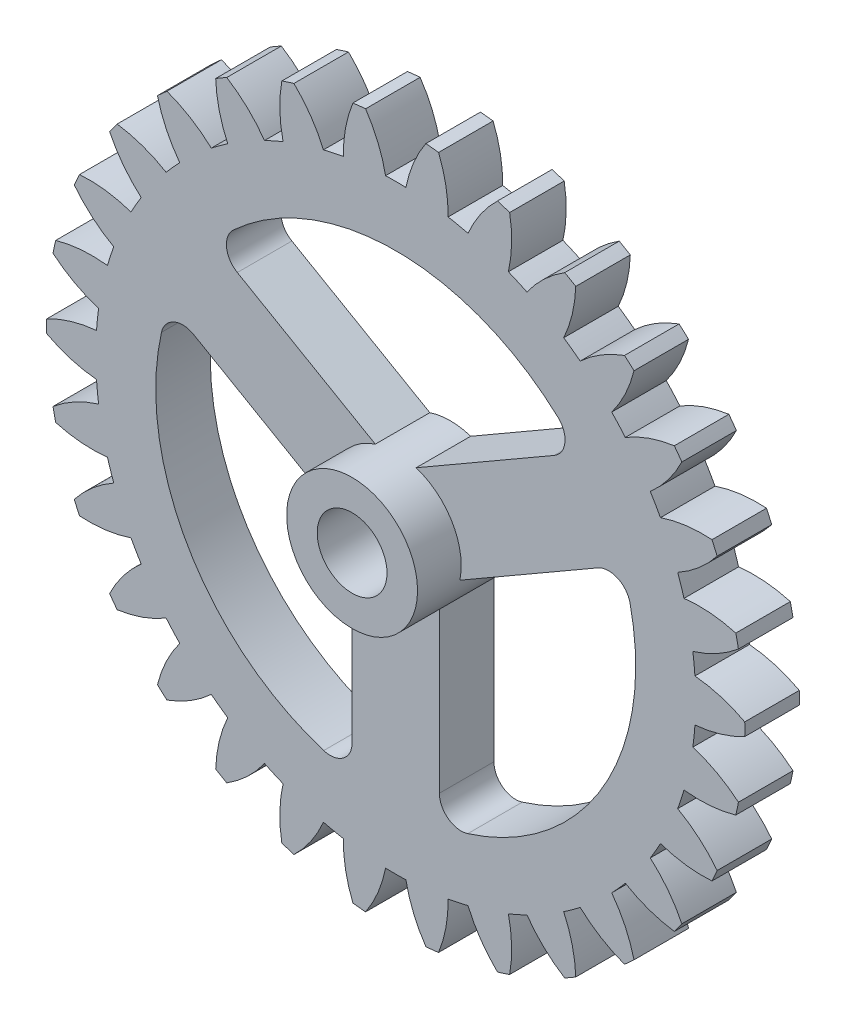
SolidWorks part; units mm, degrees
ref_plane "Front Plane" through (0, 0, 0) normal (0, 0, 1) x (1, 0, 0)
ref_plane "Top Plane" through (0, 0, 0) normal (0, 1, 0) x (1, 0, 0)
ref_plane "Right Plane" through (0, 0, 0) normal (1, 0, 0) x (0, 0, -1)
sketch "Sketch1" plane through (0, 0, 0) normal (0, 0, 1) x (1, 0, 0)
  arc A0 (-15.9973, -0.2927) -> (-13.7146, -0.9725) centre (-13.1775, 5.0034) ccw
  arc A1 (-13.7146, -0.9725) -> (-13.6171, -1.9002) centre (0, 0) ccw
  arc A2 (-13.6171, -1.9002) -> (-15.7086, -3.0398) centre (-11.8492, -7.6338) ccw
  arc A3 (-15.7086, -3.0398) -> (-15.5869, -3.6123) centre (0, 0) ccw
  arc A4 (-15.5869, -3.6123) -> (-13.2127, -3.8027) centre (-13.9298, 2.1543) ccw
  arc A5 (-13.2127, -3.8027) -> (-12.9244, -4.6898) centre (0, 0) ccw
  arc A6 (-12.9244, -4.6898) -> (-14.7333, -6.2393) centre (-10.0031, -9.9306) ccw
  arc A7 (-14.7333, -6.2393) -> (-14.4952, -6.7741) centre (0, 0) ccw
  arc A8 (-14.4952, -6.7741) -> (-12.1333, -6.4666) centre (-14.0733, -0.7889) ccw
  arc A9 (-12.1333, -6.4666) -> (-11.6669, -7.2745) centre (0, 0) ccw
  arc A10 (-11.6669, -7.2745) -> (-13.1141, -9.1662) centre (-7.7199, -11.7934) ccw
  arc A11 (-13.1141, -9.1662) -> (-12.7701, -9.6398) centre (0, 0) ccw
  arc A12 (-12.7701, -9.6398) -> (-10.5237, -8.848) centre (-13.6017, -3.6977) ccw
  arc A13 (-10.5237, -8.848) -> (-9.8995, -9.5412) centre (0, 0) ccw
  arc A14 (-9.8995, -9.5412) -> (-10.9218, -11.6925) centre (-5.0992, -13.1407) ccw
  arc A15 (-10.9218, -11.6925) -> (-10.4868, -12.0842) centre (0, 0) ccw
  arc A16 (-10.4868, -12.0842) -> (-8.4541, -10.8426) centre (-12.5357, -6.4448) ccw
  arc A17 (-8.4541, -10.8426) -> (-7.6995, -11.3909) centre (0, 0) ccw
  arc A18 (-7.6995, -11.3909) -> (-8.2521, -13.7078) centre (-2.2556, -13.9137) ccw
  arc A19 (-8.2521, -13.7078) -> (-7.7452, -14.0004) centre (0, 0) ccw
  arc A20 (-7.7452, -14.0004) -> (-6.0151, -12.3634) centre (-10.9218, -8.9103) ccw
  arc A21 (-6.0151, -12.3634) -> (-5.1629, -12.7428) centre (0, 0) ccw
  arc A22 (-5.1629, -12.7428) -> (-5.2218, -15.1239) centre (0.6865, -14.0787) ccw
  arc A23 (-5.2218, -15.1239) -> (-4.6651, -15.3048) centre (0, 0) ccw
  arc A24 (-4.6651, -15.3048) -> (-3.3131, -13.3438) centre (-8.8306, -10.9864) ccw
  arc A25 (-3.3131, -13.3438) -> (-2.4007, -13.5378) centre (0, 0) ccw
  arc A26 (-2.4007, -13.5378) -> (-1.9632, -15.8791) centre (3.5986, -13.6283) ccw
  arc A27 (-1.9632, -15.8791) -> (-1.3811, -15.9403) centre (0, 0) ccw
  arc A28 (-1.3811, -15.9403) -> (-0.4664, -13.7411) centre (-6.3534, -12.5823) ccw
  arc A29 (-0.4664, -13.7411) -> (0.4664, -13.7411) centre (0, 0) ccw
  arc A30 (0.4664, -13.7411) -> (1.3811, -15.9403) centre (6.3534, -12.5823) ccw
  arc A31 (1.3811, -15.9403) -> (1.9632, -15.8791) centre (0, 0) ccw
  arc A32 (1.9632, -15.8791) -> (2.4007, -13.5378) centre (-3.5986, -13.6283) ccw
  arc A33 (2.4007, -13.5378) -> (3.3131, -13.3438) centre (0, 0) ccw
  arc A34 (3.3131, -13.3438) -> (4.6651, -15.3048) centre (8.8306, -10.9864) ccw
  arc A35 (4.6651, -15.3048) -> (5.2218, -15.1239) centre (0, 0) ccw
  arc A36 (5.2218, -15.1239) -> (5.1629, -12.7428) centre (-0.6865, -14.0787) ccw
  arc A37 (5.1629, -12.7428) -> (6.0151, -12.3634) centre (0, 0) ccw
  arc A38 (6.0151, -12.3634) -> (7.7452, -14.0004) centre (10.9218, -8.9103) ccw
  arc A39 (7.7452, -14.0004) -> (8.2521, -13.7078) centre (0, 0) ccw
  arc A40 (8.2521, -13.7078) -> (7.6995, -11.3909) centre (2.2556, -13.9137) ccw
  arc A41 (7.6995, -11.3909) -> (8.4541, -10.8426) centre (0, 0) ccw
  arc A42 (8.4541, -10.8426) -> (10.4868, -12.0842) centre (12.5357, -6.4448) ccw
  arc A43 (10.4868, -12.0842) -> (10.9218, -11.6925) centre (0, 0) ccw
  arc A44 (10.9218, -11.6925) -> (9.8995, -9.5412) centre (5.0992, -13.1407) ccw
  arc A45 (9.8995, -9.5412) -> (10.5237, -8.848) centre (0, 0) ccw
  arc A46 (10.5237, -8.848) -> (12.7701, -9.6398) centre (13.6017, -3.6977) ccw
  arc A47 (12.7701, -9.6398) -> (13.1141, -9.1662) centre (0, 0) ccw
  arc A48 (13.1141, -9.1662) -> (11.6669, -7.2745) centre (7.7199, -11.7934) ccw
  arc A49 (11.6669, -7.2745) -> (12.1333, -6.4666) centre (0, 0) ccw
  arc A50 (12.1333, -6.4666) -> (14.4952, -6.7741) centre (14.0733, -0.7889) ccw
  arc A51 (14.4952, -6.7741) -> (14.7333, -6.2393) centre (0, 0) ccw
  arc A52 (14.7333, -6.2393) -> (12.9244, -4.6898) centre (10.0031, -9.9306) ccw
  arc A53 (12.9244, -4.6898) -> (13.2127, -3.8027) centre (0, 0) ccw
  arc A54 (13.2127, -3.8027) -> (15.5869, -3.6123) centre (13.9298, 2.1543) ccw
  arc A55 (15.5869, -3.6123) -> (15.7086, -3.0398) centre (0, 0) ccw
  arc A56 (15.7086, -3.0398) -> (13.6171, -1.9002) centre (11.8492, -7.6338) ccw
  arc A57 (13.6171, -1.9002) -> (13.7146, -0.9725) centre (0, 0) ccw
  arc A58 (13.7146, -0.9725) -> (15.9973, -0.2927) centre (13.1775, 5.0034) ccw
  arc A59 (15.9973, -0.2927) -> (15.9973, 0.2927) centre (0, 0) ccw
  arc A60 (15.9973, 0.2927) -> (13.7146, 0.9725) centre (13.1775, -5.0034) ccw
  arc A61 (13.7146, 0.9725) -> (13.6171, 1.9002) centre (0, 0) ccw
  arc A62 (13.6171, 1.9002) -> (15.7086, 3.0398) centre (11.8492, 7.6338) ccw
  arc A63 (15.7086, 3.0398) -> (15.5869, 3.6123) centre (0, 0) ccw
  arc A64 (15.5869, 3.6123) -> (13.2127, 3.8027) centre (13.9298, -2.1543) ccw
  arc A65 (13.2127, 3.8027) -> (12.9244, 4.6898) centre (0, 0) ccw
  arc A66 (12.9244, 4.6898) -> (14.7333, 6.2393) centre (10.0031, 9.9306) ccw
  arc A67 (14.7333, 6.2393) -> (14.4952, 6.7741) centre (0, 0) ccw
  arc A68 (14.4952, 6.7741) -> (12.1333, 6.4666) centre (14.0733, 0.7889) ccw
  arc A69 (12.1333, 6.4666) -> (11.6669, 7.2745) centre (0, 0) ccw
  arc A70 (11.6669, 7.2745) -> (13.1141, 9.1662) centre (7.7199, 11.7934) ccw
  arc A71 (13.1141, 9.1662) -> (12.7701, 9.6398) centre (0, 0) ccw
  arc A72 (12.7701, 9.6398) -> (10.5237, 8.848) centre (13.6017, 3.6977) ccw
  arc A73 (10.5237, 8.848) -> (9.8995, 9.5412) centre (0, 0) ccw
  arc A74 (9.8995, 9.5412) -> (10.9218, 11.6925) centre (5.0992, 13.1407) ccw
  arc A75 (10.9218, 11.6925) -> (10.4868, 12.0842) centre (0, 0) ccw
  arc A76 (10.4868, 12.0842) -> (8.4541, 10.8426) centre (12.5357, 6.4448) ccw
  arc A77 (8.4541, 10.8426) -> (7.6995, 11.3909) centre (0, 0) ccw
  arc A78 (7.6995, 11.3909) -> (8.2521, 13.7078) centre (2.2556, 13.9137) ccw
  arc A79 (8.2521, 13.7078) -> (7.7452, 14.0004) centre (0, 0) ccw
  arc A80 (7.7452, 14.0004) -> (6.0151, 12.3634) centre (10.9218, 8.9103) ccw
  arc A81 (6.0151, 12.3634) -> (5.1629, 12.7428) centre (0, 0) ccw
  arc A82 (5.1629, 12.7428) -> (5.2218, 15.1239) centre (-0.6865, 14.0787) ccw
  arc A83 (5.2218, 15.1239) -> (4.6651, 15.3048) centre (0, 0) ccw
  arc A84 (4.6651, 15.3048) -> (3.3131, 13.3438) centre (8.8306, 10.9864) ccw
  arc A85 (3.3131, 13.3438) -> (2.4007, 13.5378) centre (0, 0) ccw
  arc A86 (2.4007, 13.5378) -> (1.9632, 15.8791) centre (-3.5986, 13.6283) ccw
  arc A87 (1.9632, 15.8791) -> (1.3811, 15.9403) centre (0, 0) ccw
  arc A88 (1.3811, 15.9403) -> (0.4664, 13.7411) centre (6.3534, 12.5823) ccw
  arc A89 (0.4664, 13.7411) -> (-0.4664, 13.7411) centre (0, 0) ccw
  arc A90 (-0.4664, 13.7411) -> (-1.3811, 15.9403) centre (-6.3534, 12.5823) ccw
  arc A91 (-1.3811, 15.9403) -> (-1.9632, 15.8791) centre (0, 0) ccw
  arc A92 (-1.9632, 15.8791) -> (-2.4007, 13.5378) centre (3.5986, 13.6283) ccw
  arc A93 (-2.4007, 13.5378) -> (-3.3131, 13.3438) centre (0, 0) ccw
  arc A94 (-3.3131, 13.3438) -> (-4.6651, 15.3048) centre (-8.8306, 10.9864) ccw
  arc A95 (-4.6651, 15.3048) -> (-5.2218, 15.1239) centre (0, 0) ccw
  arc A96 (-5.2218, 15.1239) -> (-5.1629, 12.7428) centre (0.6865, 14.0787) ccw
  arc A97 (-5.1629, 12.7428) -> (-6.0151, 12.3634) centre (0, 0) ccw
  arc A98 (-6.0151, 12.3634) -> (-7.7452, 14.0004) centre (-10.9218, 8.9103) ccw
  arc A99 (-7.7452, 14.0004) -> (-8.2521, 13.7078) centre (0, 0) ccw
  arc A100 (-8.2521, 13.7078) -> (-7.6995, 11.3909) centre (-2.2556, 13.9137) ccw
  arc A101 (-7.6995, 11.3909) -> (-8.4541, 10.8426) centre (0, 0) ccw
  arc A102 (-8.4541, 10.8426) -> (-10.4868, 12.0842) centre (-12.5357, 6.4448) ccw
  arc A103 (-10.4868, 12.0842) -> (-10.9218, 11.6925) centre (0, 0) ccw
  arc A104 (-10.9218, 11.6925) -> (-9.8995, 9.5412) centre (-5.0992, 13.1407) ccw
  arc A105 (-9.8995, 9.5412) -> (-10.5237, 8.848) centre (0, 0) ccw
  arc A106 (-10.5237, 8.848) -> (-12.7701, 9.6398) centre (-13.6017, 3.6977) ccw
  arc A107 (-12.7701, 9.6398) -> (-13.1141, 9.1662) centre (0, 0) ccw
  arc A108 (-13.1141, 9.1662) -> (-11.6669, 7.2745) centre (-7.7199, 11.7934) ccw
  arc A109 (-11.6669, 7.2745) -> (-12.1333, 6.4666) centre (0, 0) ccw
  arc A110 (-12.1333, 6.4666) -> (-14.4952, 6.7741) centre (-14.0733, 0.7889) ccw
  arc A111 (-14.4952, 6.7741) -> (-14.7333, 6.2393) centre (0, 0) ccw
  arc A112 (-14.7333, 6.2393) -> (-12.9244, 4.6898) centre (-10.0031, 9.9306) ccw
  arc A113 (-12.9244, 4.6898) -> (-13.2127, 3.8027) centre (0, 0) ccw
  arc A114 (-13.2127, 3.8027) -> (-15.5869, 3.6123) centre (-13.9298, -2.1543) ccw
  arc A115 (-15.5869, 3.6123) -> (-15.7086, 3.0398) centre (0, 0) ccw
  arc A116 (-15.7086, 3.0398) -> (-13.6171, 1.9002) centre (-11.8492, 7.6338) ccw
  arc A117 (-13.6171, 1.9002) -> (-13.7146, 0.9725) centre (0, 0) ccw
  arc A118 (-13.7146, 0.9725) -> (-15.9973, 0.2927) centre (-13.1775, -5.0034) ccw
  arc A119 (-15.9973, 0.2927) -> (-15.9973, -0.2927) centre (0, 0) ccw
extrude "Boss-Extrude1" add sketch "Sketch1" along normal mid plane 2.5
sketch "Sketch2" plane through (0, 0, 1.25) normal (0, 0, 1) x (1, 0, 0)
  line L0 (0, 25.5287) -> (0, -28.5276) construction
  line L1 (-31.2958, 0) -> (22.6068, 0) construction
  line L2 (0, -15) -> (3.8007, -15) construction
  circle A0 centre (0, 0) radius 15 construction
  circle A1 centre (0, 0) radius 16 construction
  dimension "D1" = 30
sketch "Sketch3" plane through (0, 0, 1.25) normal (0, 0, 1) x (1, 0, 0)
  circle A0 centre (0, 0) radius 1.5
  dimension "D1" = 3
extrude "Cut-Extrude1" cut sketch "Sketch3" against normal through all
sketch "Sketch4" plane through (0, 0, 1.25) normal (0, 0, 1) x (1, 0, 0)
  line L0 (0, 23.917) -> (0, -20.8905) construction
  line L1 (-28.5676, 0) -> (24.3599, 0) construction
  line L2 (0.9365, 2.8501) -> (7.2614, 6.5017)
  line L3 (8.3675, 7.1404) -> (2.3703, 14.1682) construction
  line L4 (-0.9365, 2.8501) -> (-7.2614, 6.5017)
  line L5 (2, -2.2361) -> (2, -9.5394)
  line L6 (2.9365, -0.614) -> (9.2614, 3.0376)
  line L7 (2, -10.8167) -> (11.0848, -9.1369) construction
  line L8 (-2.9365, -0.614) -> (-9.2614, 3.0376)
  line L9 (-2, -2.2361) -> (-2, -9.5394)
  line L10 (-10.3675, 3.6763) -> (-13.4552, -5.0313) construction
  line L11 (0, 0) -> (10.1712, 5.8724) construction
  arc A0 (-7.4375, 8.1045) -> (7.4375, 8.1045) centre (0, 0) cw
  arc A1 (-0.9365, 2.8501) -> (0.9365, 2.8501) centre (0, 0) cw
  arc A2 (10.7375, 2.3888) -> (3.3, -10.4933) centre (0, 0) cw
  arc A3 (2.9365, -0.614) -> (2, -2.2361) centre (0, 0) cw
  arc A4 (-3.3, -10.4933) -> (-10.7375, 2.3888) centre (0, 0) cw
  arc A5 (-2, -2.2361) -> (-2.9365, -0.614) centre (0, 0) cw
  arc A6 (7.4375, 8.1045) -> (7.2614, 6.5017) centre (6.7614, 7.3678) cw
  arc A7 (9.2614, 3.0376) -> (10.7375, 2.3888) centre (9.7614, 2.1716) cw
  arc A8 (2, -9.5394) -> (3.3, -10.4933) centre (3, -9.5394) ccw
  arc A9 (-2, -9.5394) -> (-3.3, -10.4933) centre (-3, -9.5394) cw
  arc A10 (-9.2614, 3.0376) -> (-10.7375, 2.3888) centre (-9.7614, 2.1716) ccw
  arc A11 (-7.2614, 6.5017) -> (-7.4375, 8.1045) centre (-6.7614, 7.3678) cw
  point P24 (0, 0)
  point P38 (-8.3675, 7.1404)
  dimension "D3" = 3
  dimension "D4" = 11
  dimension "D6" = 1
  dimension "D1" = 4
  dimension "D5" = 30
  dimension "D2" = 3
extrude "Cut-Extrude2" cut sketch "Sketch4" against normal through all
sketch "Sketch5" plane through (0, 0, 1.25) normal (0, 0, 1) x (1, 0, 0)
  circle A0 centre (0, 0) radius 3
  circle A1 centre (0, 0) radius 1.5 construction
  circle A2 centre (0, 0) radius 1.5
extrude "Boss-Extrude2" add sketch "Sketch5" along normal blind 2
sketch "Sketch6" plane through (0, 0, 3.25) normal (0, 0, 1) x (1, 0, 0)
  circle A0 centre (0, 0) radius 1.6
  dimension "D1" = 3.2
extrude "Cut-Extrude3" cut sketch "Sketch6" against normal through all
